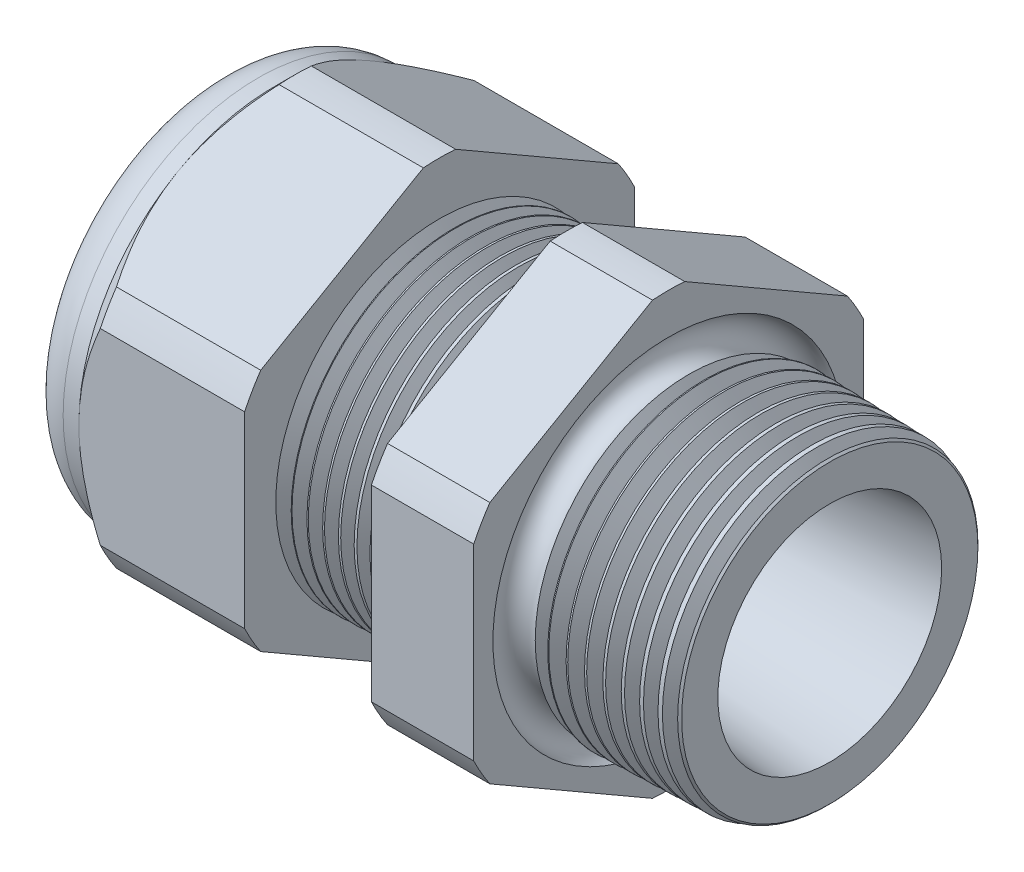
SolidWorks part; units mm, degrees
ref_plane "Front Plane" through (0, 0, 0) normal (0, 0, 1) x (1, 0, 0)
ref_plane "Top Plane" through (0, 0, 0) normal (0, 1, 0) x (1, 0, 0)
ref_plane "Right Plane" through (0, 0, 0) normal (1, 0, 0) x (0, 0, -1)
sketch "Sketch10" plane through (0, 0, 0) normal (0, 0, 1) x (1, 0, 0)
  line L0 (0, 0) -> (-115.3565, 0) construction
  line L1 (-29.972, 3.937) -> (-19.072, 3.937)
  line L2 (0, 5.4696) -> (0, 7.5016)
  line L3 (-7.874, 7.7078) -> (0, 7.5016)
  line L4 (-7.874, 19.05) -> (-7.874, 7.7078)
  line L5 (-7.874, 19.05) -> (-12.874, 19.05)
  line L6 (-12.874, 19.05) -> (-12.874, 7.8387)
  line L7 (-19.072, 8.001) -> (-12.874, 7.8387)
  line L8 (-19.072, 8.001) -> (-19.072, 19.05)
  line L9 (-19.072, 19.05) -> (-27.172, 19.05)
  line L10 (-27.172, 19.05) -> (-27.172, 9.525)
  line L11 (-27.172, 9.525) -> (-29.972, 9.525)
  line L12 (-29.972, 9.525) -> (-29.972, 3.937)
  line L13 (-19.072, 3.937) -> (0, 5.4696)
  dimension "D1" = 29.972
  dimension "D2" = 7.874
  dimension "D3" = 1.5
  dimension "D4" = 2.032
  dimension "A" = 16.002
  dimension "D6" = 19.05
  dimension "D8" = 38.1
  dimension "D9" = 2.8
  dimension "D10" = 8.1
  dimension "D11" = 5
  dimension "D" = 7.874
revolve "Revolve2" add sketch "Sketch10" angle 360 about L0
sketch "Sketch12" plane through (-27.172, 0, 0) normal (-1, 0, 0) x (0, 0, 1)
  line L1 (-0.7885, 10.5433) -> (-8.7365, 5.9545)
  line L2 (-9.525, 4.5888) -> (-9.525, -4.5888)
  line L3 (-8.7365, -5.9545) -> (-0.7885, -10.5433)
  line L4 (0.7885, -10.5433) -> (8.7365, -5.9545)
  line L5 (9.525, -4.5888) -> (9.525, 4.5888)
  line L6 (8.7365, 5.9545) -> (0.7885, 10.5433)
  circle A0 centre (0, 0) radius 9.525 construction
  arc A1 (0.7885, 10.5433) -> (-0.7885, 10.5433) centre (0, 0) ccw
  arc A2 (-8.7365, 5.9545) -> (-9.525, 4.5888) centre (0, 0) ccw
  arc A3 (-9.525, -4.5888) -> (-8.7365, -5.9545) centre (0, 0) ccw
  arc A4 (-0.7885, -10.5433) -> (0.7885, -10.5433) centre (0, 0) ccw
  arc A5 (8.7365, -5.9545) -> (9.525, -4.5888) centre (0, 0) ccw
  arc A6 (9.525, 4.5888) -> (8.7365, 5.9545) centre (0, 0) ccw
  dimension "D2" = 21.1455
  dimension "D1" = 19.05
extrude "Cut-Extrude2" cut sketch "Sketch12" against normal through all flip side to cut
fillet "Fillet4" radius 2.032 1 edges at (-29.972, 0, -9.525)
sketch "Sketch19" plane through (-27.172, 0, 0) normal (-1, 0, 0) x (0, 0, 1)
  line L0 (9.525, 0) -> (9.525, 4.5888) construction
  circle A0 centre (0, 0) radius 9.525
extrude "Cut-Extrude3" cut sketch "Sketch19" against normal blind 2 draft 45 flip side to cut
chamfer "Chamfer1" distance 0.254 angle 45 1 edges at (0, 0, -7.5016)
sketch "Sketch21" plane through (-29.972, 0, 0) normal (-1, 0, 0) x (0, 0, 1)
  circle A0 centre (0, 0) radius 3.937
  circle A2 centre (0, 0) radius 3.937 construction
extrude "plug" add sketch "Sketch21" against normal blind 3.81 separate body
sketch "Sketch22" plane through (-29.972, 0, 0) normal (-1, 0, 0) x (0, 0, 1)
  circle A0 centre (0, 0) radius 3.683
  circle A1 centre (0, 0) radius 3.937 construction
  dimension "D1" = 0.254
extrude "Cut-Extrude4" cut sketch "Sketch22" against normal blind 0.508
sketch "Sketch27" plane through (-29.464, 0, 0) normal (-1, 0, 0) x (0, 0, 1)
  line L0 (-4.3624, 0) -> (4.3624, 0) construction
  circle A0 centre (-2.918, 0) radius 0.762
  circle A1 centre (0, 0) radius 3.683 construction
  dimension "D1" = 0.003
  dimension "holedia" = 1.524
extrude "plugholes" cut sketch "Sketch27" against normal through all
pattern_circular "CirPattern1" count 4 over 360 about axis through (0, 0, 0) along (1, 0, 0) of "plugholes"
sketch "Sketch28" plane through (-29.464, 0, 0) normal (-1, 0, 0) x (0, 0, 1)
  circle A0 centre (0, 0) radius 0.762
  dimension "midholedia" = 1.524
extrude "midhole" cut sketch "Sketch28" against normal through all
sketch "Sketch29" plane through (0, 0, 0) normal (0, 0, 1) x (1, 0, 0)
  line L0 (-19.072, 8.001) -> (-18.339, 7.9818)
  line L1 (-12.874, 7.8387) -> (-19.072, 8.001) construction
  line L2 (-18.339, 7.9818) -> (-18.7221, 7.3566)
  line L3 (-18.7221, 7.3566) -> (-19.072, 8.001)
  dimension "D1" = 60
  dimension "D2" = 60
  dimension "D3" = 0.635
revolve "Cut-Revolve1" cut sketch "Sketch29" angle 360 about axis through (0, 0, 0) along (-1, 0, 0)
pattern_linear "LPattern1" count 8 spacing 0.762 along (1, 0, 0) of "Cut-Revolve1"
sketch "Sketch30" plane through (0, 0, 0) normal (0, 0, 1) x (1, 0, 0)
  line L0 (-7.874, 7.7078) -> (-6.9944, 7.6847)
  line L1 (-7.874, 10.5433) -> (-7.874, 5.9545) construction
  line L2 (-0.2539, 7.5082) -> (-7.874, 7.7078) construction
  line L3 (-6.9944, 7.6847) -> (-7.4542, 6.9345)
  line L4 (-7.4542, 6.9345) -> (-7.874, 7.7078)
  dimension "D1" = 60
  dimension "D2" = 60
  dimension "D3" = 0.762
revolve "Cut-Revolve2" cut sketch "Sketch30" angle 360 about axis through (0, 0, 0) along (-1, 0, 0)
pattern_linear "LPattern2" count 9 spacing 0.889 along (1, 0, 0) of "Cut-Revolve2"
sketch "Sketch31" [suppressed] plane through (-38.354, 0, 0) normal (-1, 0, 0) x (0, 0, 1)
  line L0 (-1.905, 1.905) -> (1.905, 1.905)
  line L1 (-1.905, -1.905) -> (1.905, -1.905)
  circle A0 centre (0, 0) radius 1.905 construction
  arc A1 (-1.905, 1.905) -> (-1.905, -1.905) centre (-1.905, 0) ccw
  arc A2 (1.905, 1.905) -> (1.905, -1.905) centre (1.905, 0) cw
extrude "Cut-Extrude5" [suppressed] cut sketch "Sketch31" against normal through all
sketch "Sketch32" plane through (0, 0, 0) normal (0, 0, 1) x (1, 0, 0)
  line L0 (-7.874, 10.5433) -> (-7.874, 5.9545) construction
  circle A0 centre (-7.747, 7.7078) radius 0.889
  dimension "D2" = 1.778
  dimension "D1" = 0.127
revolve "Cut-Revolve3" cut sketch "Sketch32" angle 360 about axis through (0, 0, 0) along (-1, 0, 0)
